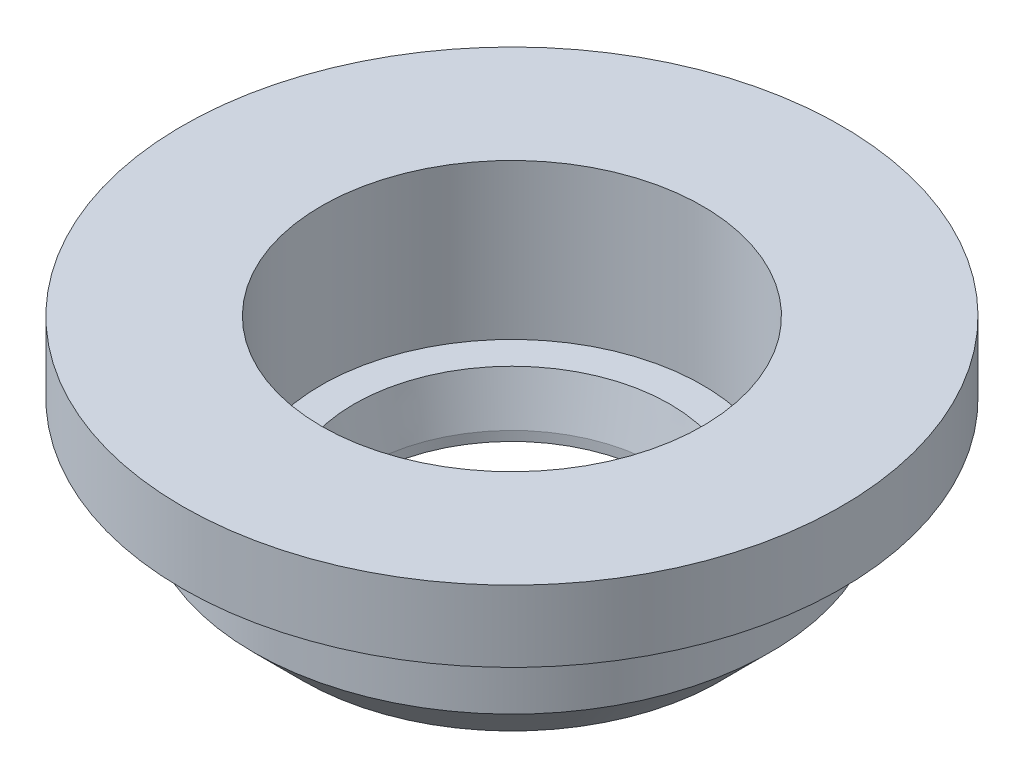
SolidWorks part; units mm, degrees
ref_plane "Front Plane" through (0, 0, 0) normal (0, 0, 1) x (1, 0, 0)
ref_plane "Top Plane" through (0, 0, 0) normal (0, 1, 0) x (1, 0, 0)
ref_plane "Right Plane" through (0, 0, 0) normal (1, 0, 0) x (0, 0, -1)
sketch "Sketch1" plane through (0, 0, 0) normal (0, 0, 1) x (1, 0, 0)
  line L0 (5.087, 2.8701) -> (5.5245, 4.6733) construction
  line L1 (-6.6675, 4.6733) -> (6.6675, 4.6733) construction
  line L2 (6.6675, 4.6733) -> (6.6675, 5.3083) construction
  line L4 (5.087, 2.8701) -> (5.5245, 4.6733) construction
  line L5 (5.5245, 4.6733) -> (6.6675, 4.6733) construction
  line L6 (6.6675, 4.6733) -> (6.6675, 5.3083) construction
  line L7 (6.6675, 10.0708) -> (6.7945, 10.0708) construction
  line L8 (5.087, 2.8701) -> (5.087, 2.5143) construction
  line L9 (4.6345, 2.5143) -> (5.087, 2.5143) construction
  line L10 (-4.6345, 2.5143) -> (4.6345, 2.5143) construction
  line L11 (5.087, 2.5143) -> (5.214, 2.5143) construction
  line L12 (9.2075, 4.2923) -> (9.2075, 7.5308)
  line L13 (4.7625, 10.0708) -> (-4.7625, 10.0708) construction
  line L14 (5.214, 2.8549) -> (5.214, 2.5143)
  line L15 (7.4295, 2.5143) -> (9.2075, 4.2923)
  line L16 (6.6675, 5.3083) -> (6.6675, 10.0708) construction
  line L17 (5.214, 2.8549) -> (5.6244, 4.5463)
  line L18 (5.6244, 4.5463) -> (6.7945, 4.5463)
  line L19 (6.7945, 4.5463) -> (6.7945, 5.3083)
  line L20 (6.7945, 5.3083) -> (6.7945, 10.0708)
  line L21 (5.214, 2.5143) -> (7.4295, 2.5143)
  line L22 (6.7945, 10.0708) -> (8.89, 10.0708)
  line L24 (8.89, 10.0708) -> (11.7475, 10.0708)
  line L26 (9.2075, 7.5308) -> (11.7475, 7.5308)
  line L27 (11.7475, 10.0708) -> (11.7475, 7.5308)
  arc A1 (4.6345, 2.5143) -> (5.087, 2.8701) centre (4.6345, 2.9799) ccw construction
  point P6 (9.2075, 2.5143)
  dimension "D1" = 2.54
  dimension "D2" = 0.127
  dimension "D3" = 2.54
  dimension "D4" = 2.54
ref_axis "Axis1" through (0, 10.4486, 0) along (0, -1, 0)
revolve "Revolve1" add sketch "Sketch1" angle 360 about axis through (0, 10.4486, 0) along (0, -1, 0)
